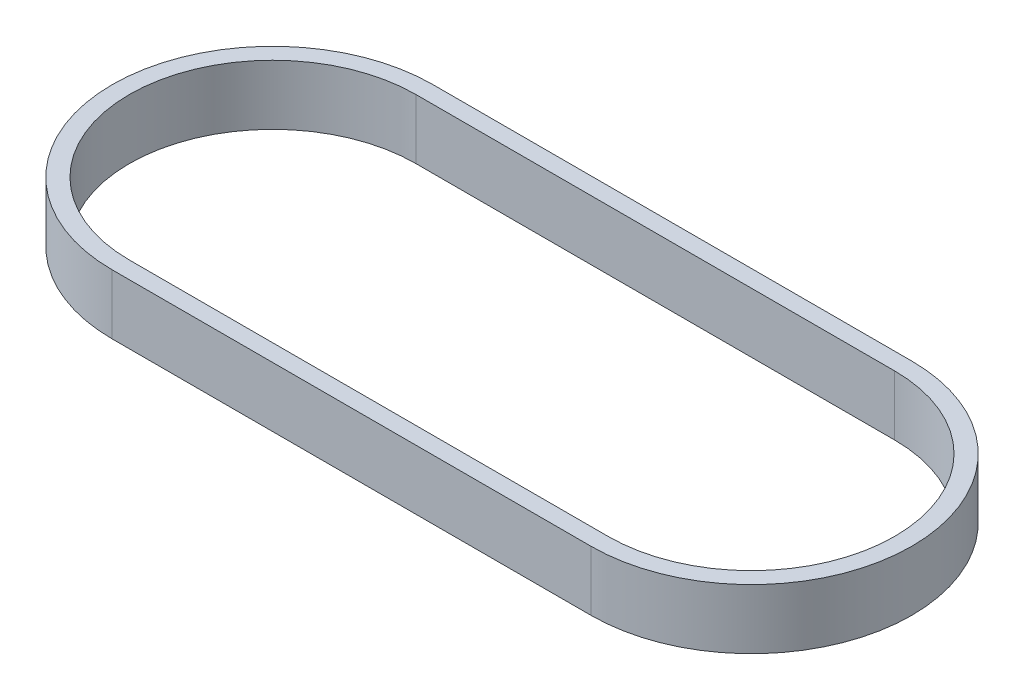
SolidWorks part; units mm, degrees
ref_plane "前视基准面" through (0, 0, 0) normal (0, 0, 1) x (1, 0, 0)
ref_plane "上视基准面" through (0, 0, 0) normal (0, 1, 0) x (1, 0, 0)
ref_plane "右视基准面" through (0, 0, 0) normal (1, 0, 0) x (0, 0, -1)
sketch "草图2" plane through (0, 0, 0) normal (0, 1, 0) x (1, 0, 0)
  line L0 (0, 0) -> (56, 0) construction
  line L1 (0, 17.76) -> (56, 17.76)
  line L2 (0, -17.76) -> (56, -17.76)
  arc A0 (0, 17.76) -> (0, -17.76) centre (0, 0) ccw
  arc A1 (56, -17.76) -> (56, 17.76) centre (56, 0) ccw
  dimension "D2" = 35.52
  dimension "D1" = 56
extrude "拉伸-薄壁1" add sketch "草图2" along normal blind 7 thin thin type mid plane wall 2
